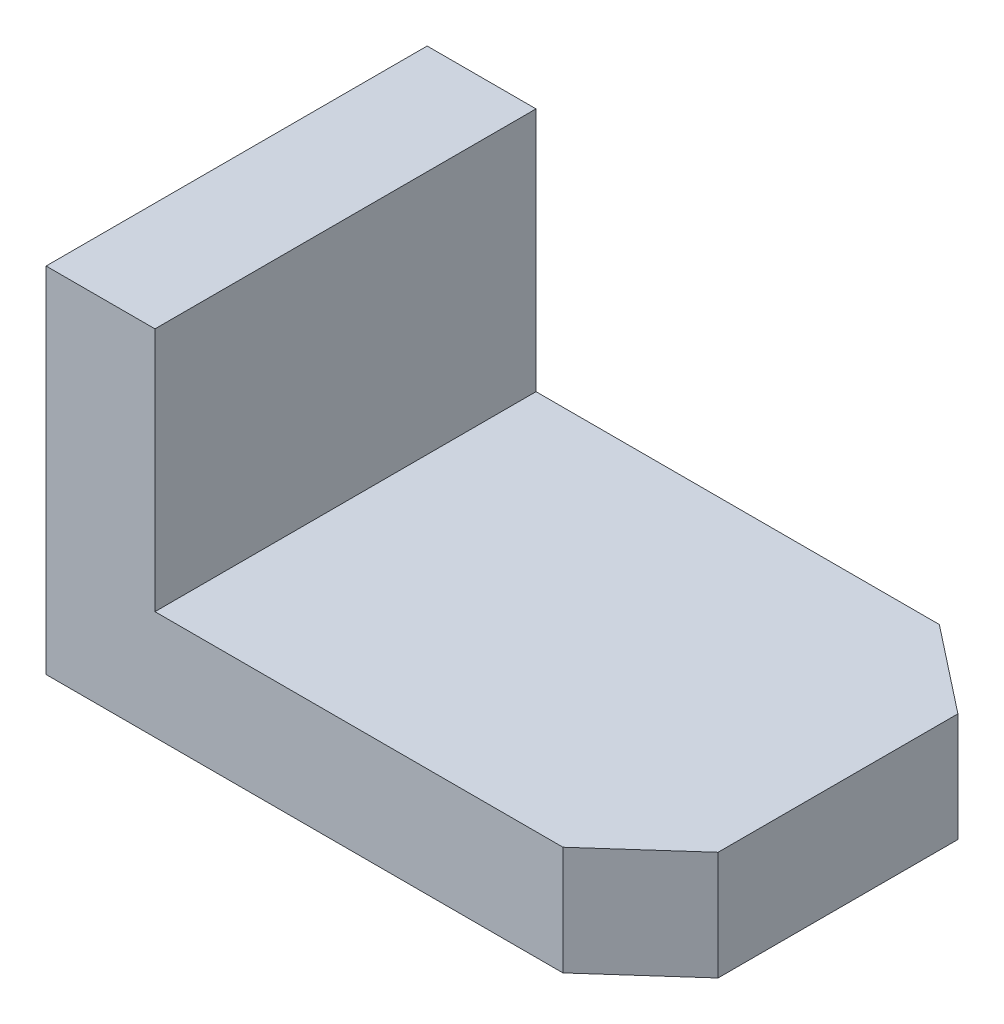
SolidWorks part; units mm, degrees
ref_plane "Front Plane" through (0, 0, 0) normal (0, 0, 1) x (1, 0, 0)
ref_plane "Top Plane" through (0, 0, 0) normal (0, 1, 0) x (1, 0, 0)
ref_plane "Right Plane" through (0, 0, 0) normal (1, 0, 0) x (0, 0, -1)
sketch "Sketch1" plane through (0, 0, 0) normal (0, 1, 0) x (1, 0, 0)
  line L1 (-33, 21) -> (33, 21)
  line L2 (-33, 21) -> (-33, -21)
  line L3 (-33, -21) -> (33, -21)
  line L4 (33, 21) -> (33, -21)
  line L5 (-33, 21) -> (33, -21) construction
  line L6 (-33, -21) -> (33, 21) construction
  point P0 (0, 0)
  dimension "D1" = 66
  dimension "D2" = 42
extrude "Boss-Extrude1" add sketch "Sketch1" along normal blind 12 contours L2 L3 L4 L1
sketch "Sketch2" plane through (0, 12, 0) normal (0, 1, 0) x (1, 0, 0)
  line L0 (-33, 21) -> (-33, -21) construction
  line L1 (-33, -21) -> (33, -21) construction
  line L2 (-33, 21) -> (-21, 21)
  line L3 (-33, 21) -> (-33, -21)
  line L4 (-33, -21) -> (-21, -21)
  line L5 (-21, 21) -> (-21, -21)
  dimension "D1" = 12
extrude "Boss-Extrude2" add sketch "Sketch2" along normal blind 26.995
sketch "Sketch12" plane through (0, 12, 0) normal (0, 1, 0) x (1, 0, 0)
  line L0 (33, -12.9358) -> (33, -21)
  line L1 (33, -21) -> (23.9654, -21)
  line L2 (33, 13.5) -> (33, 21)
  line L3 (33, 21) -> (23.4551, 21)
  line L4 (-21, 21) -> (33, 21) construction
  line L5 (23.9654, -21) -> (33, -12.9358)
  line L6 (33, 13.5) -> (23.4551, 21)
extrude "Cut-Extrude1" cut sketch "Sketch12" against normal blind 12
